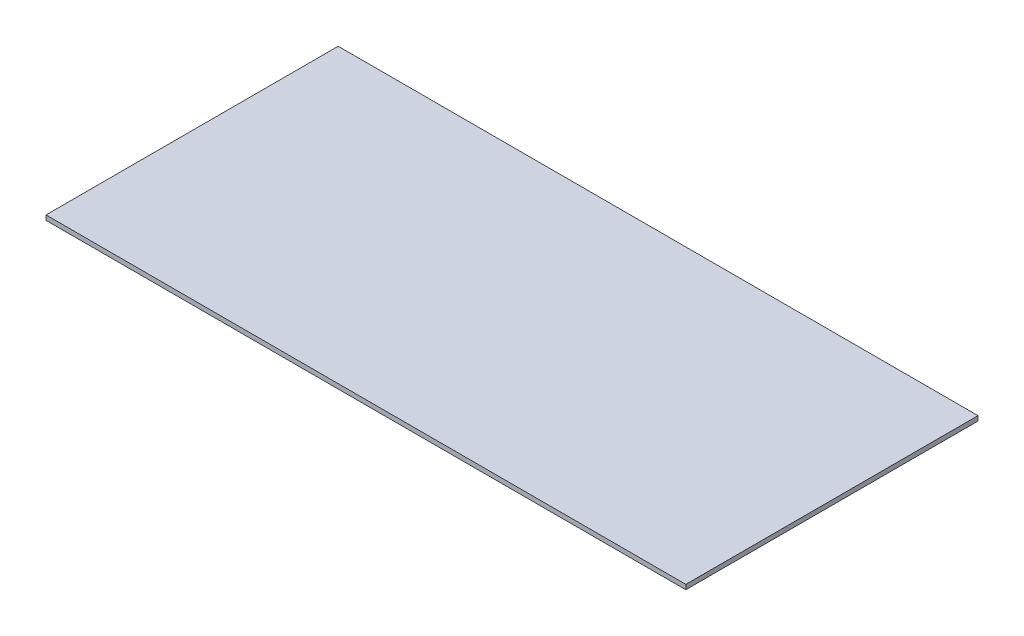
SolidWorks part; units mm, degrees
material "Mahogany"
ref_plane "Front Plane" through (0, 0, 0) normal (0, 0, 1) x (1, 0, 0)
ref_plane "Top Plane" through (0, 0, 0) normal (0, 1, 0) x (1, 0, 0)
ref_plane "Right Plane" through (0, 0, 0) normal (1, 0, 0) x (0, 0, -1)
sketch "Sketch1" plane through (0, 0, 0) normal (0, 1, 0) x (1, 0, 0)
  line L1 (865, -395) -> (-865, -395)
  line L2 (865, -395) -> (865, 395)
  line L3 (865, 395) -> (-865, 395)
  line L4 (-865, -395) -> (-865, 395)
  line L5 (865, -395) -> (-865, 395) construction
  line L6 (865, 395) -> (-865, -395) construction
  point P0 (0, 0)
  dimension "D1" = 1730
  dimension "D2" = 790
extrude "Boss-Extrude1" add sketch "Sketch1" along normal blind 12.7
equation "\"W\"= 1700"
equation "\"L\"= 760"
equation "\"H\"= 810"
equation "\"ARM_BOLT_SPACING\"= 166"
equation "\"ARM_TO_WALL\"= 300"
equation "\"D1@Sketch1\"=\"W\"+30"
equation "\"D2@Sketch1\"=\"L\"+30"
